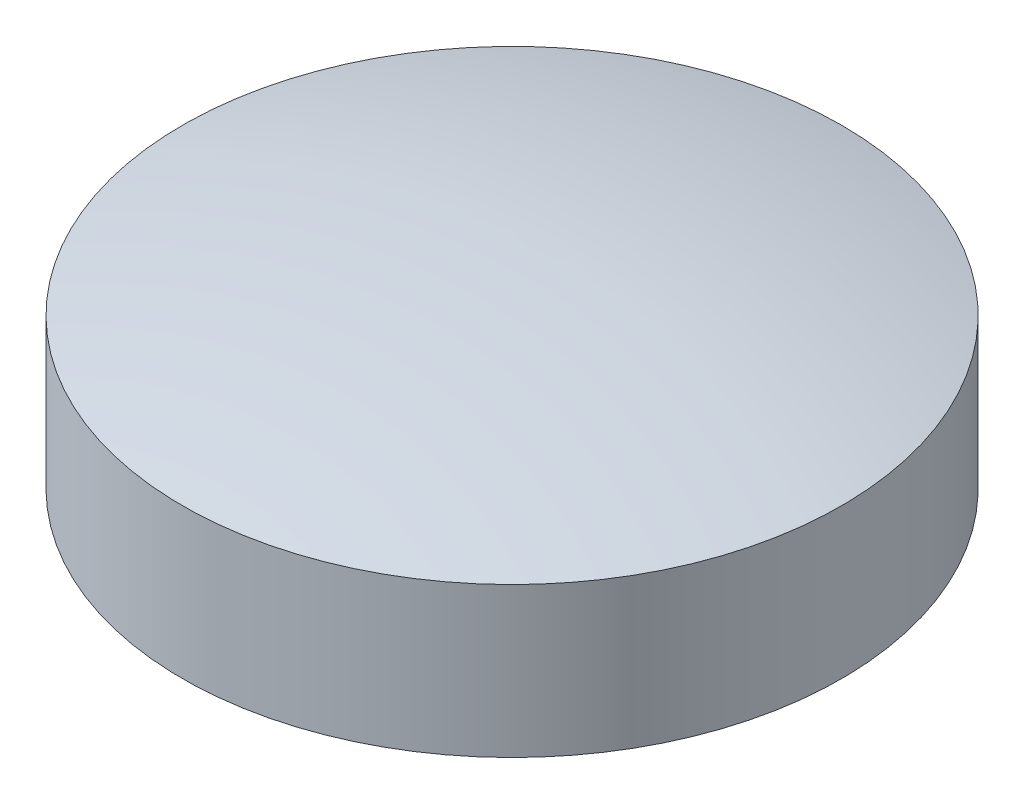
SolidWorks part; units mm, degrees
ref_plane "Front Plane" through (0, 0, 0) normal (0, 0, 1) x (1, 0, 0)
ref_plane "Top Plane" through (0, 0, 0) normal (0, 1, 0) x (1, 0, 0)
ref_plane "Right Plane" through (0, 0, 0) normal (1, 0, 0) x (0, 0, -1)
sketch "Sketch2" plane through (0, 0, 0) normal (1, 0, 0) x (0, 0, -1)
  line L0 (0, 0) -> (0, 44.0732) construction
  line L1 (0, 0) -> (22, 0)
  line L2 (22, 0) -> (22, 10)
  line L3 (0, 0) -> (0, 13)
  arc A0 (0, 13) -> (22, 10) centre (0, -69.1667) cw
  dimension "D1" = 13
  dimension "D2" = 3
  dimension "D3" = 44
revolve "Revolve1" add sketch "Sketch2" angle 360 about L0
